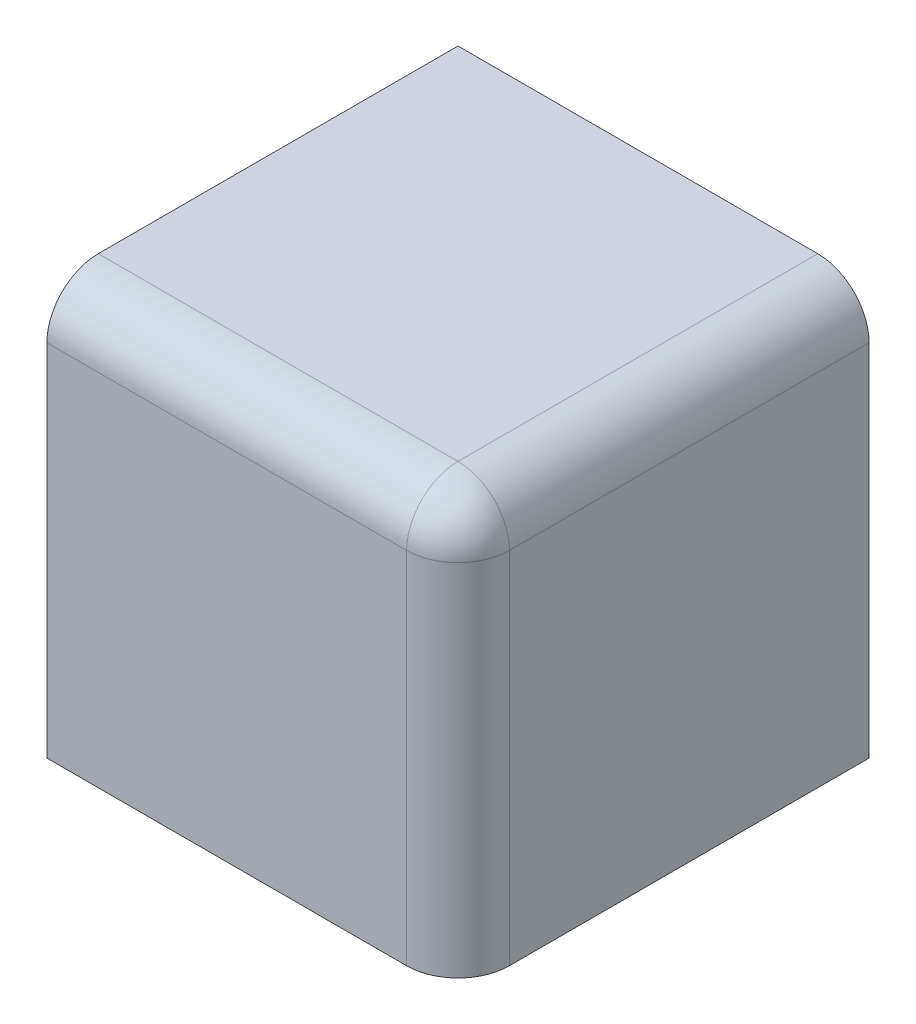
SolidWorks part; units mm, degrees
ref_plane "Front Plane" through (0, 0, 0) normal (0, 0, 1) x (1, 0, 0)
ref_plane "Top Plane" through (0, 0, 0) normal (0, 1, 0) x (1, 0, 0)
ref_plane "Right Plane" through (0, 0, 0) normal (1, 0, 0) x (0, 0, -1)
ref_plane "Plane1" through (0, 20, 0) normal (0, 1, 0) x (1, 0, 0)
sketch "Sketch1" plane through (0, 20, 0) normal (0, 1, 0) x (1, 0, 0)
  line L0 (20, -20) -> (20, 0)
  line L1 (20, 0) -> (0, 0)
  line L2 (0, 0) -> (0, -20)
  line L3 (0, -20) -> (20, -20)
extrude "Boss-Extrude1" add sketch "Sketch1" against normal blind 20
sketch "Sketch2" plane through (0, 0, 0) normal (0, 0, -1) x (-1, 0, 0)
  line L0 (0, 0) -> (0, 17.5)
  line L1 (0, 17.5) -> (-17.5, 17.5)
  line L2 (-17.5, 17.5) -> (-17.5, 0)
  line L3 (-17.5, 0) -> (0, 0)
extrude "Cut-Extrude1" cut sketch "Sketch2" against normal blind 17.5
fillet "Fillet1" radius 2.5 3 edges at (20, 20, 10) (10, 20, 20) (20, 10, 20)
